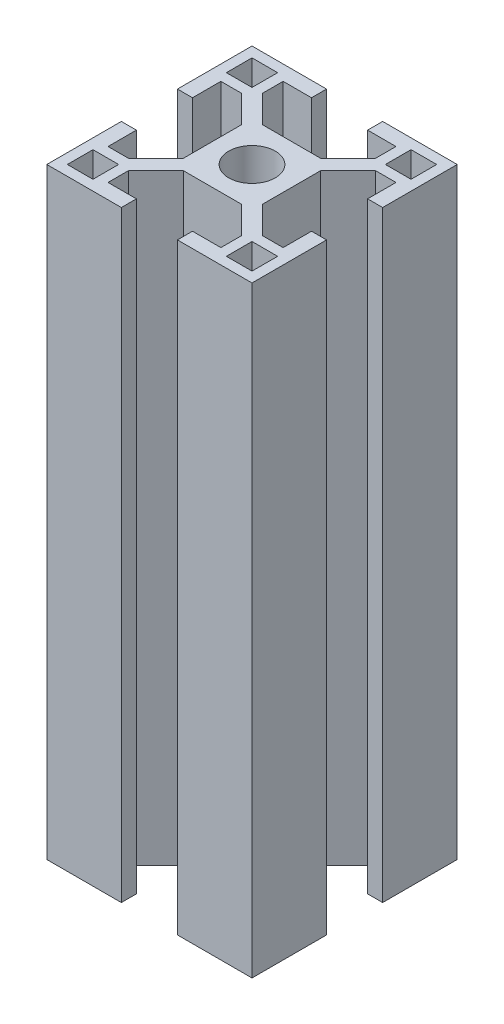
SolidWorks part; units mm, degrees
ref_plane "Płaszczyzna przednia" through (0, 0, 0) normal (0, 0, 1) x (1, 0, 0)
ref_plane "Płaszczyzna górna" through (0, 0, 0) normal (0, 1, 0) x (1, 0, 0)
ref_plane "Płaszczyzna prawa" through (0, 0, 0) normal (1, 0, 0) x (0, 0, -1)
sketch "Szkic1" plane through (0, 0, 0) normal (0, 1, 0) x (1, 0, 0)
  line L0 (4.1, 15) -> (4.1, 12.8)
  line L1 (-4.2444, -5.8) -> (4.2444, -5.8)
  line L2 (-5.8, -4.2444) -> (-5.8, 4.2444)
  line L3 (-4.2444, 5.8) -> (4.2444, 5.8)
  line L4 (5.8, -4.2444) -> (5.8, 4.2444)
  line L5 (-15, -15) -> (15, 15) construction
  line L6 (-15, 15) -> (15, -15) construction
  line L7 (4.1, 12.8) -> (8.25, 12.8)
  line L8 (8.25, 12.8) -> (8.25, 9.8056)
  line L9 (8.25, 9.8056) -> (4.2444, 5.8)
  line L10 (4.1, 15) -> (15, 15)
  line L11 (15, 15) -> (15, 4.1)
  line L12 (15, 4.1) -> (12.8, 4.1)
  line L13 (12.8, 4.1) -> (12.8, 8.25)
  line L14 (12.8, 8.25) -> (9.8056, 8.25)
  line L15 (9.8056, 8.25) -> (5.8, 4.2444)
  line L16 (-21.1799, 0) -> (30.3897, 0) construction
  line L17 (4.1, -15) -> (4.1, -12.8)
  line L18 (9.8056, -8.25) -> (5.8, -4.2444)
  line L19 (12.8, -8.25) -> (9.8056, -8.25)
  line L20 (12.8, -4.1) -> (12.8, -8.25)
  line L21 (15, -4.1) -> (12.8, -4.1)
  line L22 (15, -15) -> (15, -4.1)
  line L23 (4.1, -15) -> (15, -15)
  line L24 (8.25, -9.8056) -> (4.2444, -5.8)
  line L25 (8.25, -12.8) -> (8.25, -9.8056)
  line L26 (4.1, -12.8) -> (8.25, -12.8)
  line L27 (0, 19.5766) -> (0, -23.5143) construction
  line L28 (-4.1, 15) -> (-15, 15)
  line L29 (-4.1, 15) -> (-4.1, 12.8)
  line L30 (-8.25, 9.8056) -> (-4.2444, 5.8)
  line L31 (-8.25, 12.8) -> (-8.25, 9.8056)
  line L32 (-4.1, 12.8) -> (-8.25, 12.8)
  line L33 (-9.8056, 8.25) -> (-5.8, 4.2444)
  line L34 (-12.8, 8.25) -> (-9.8056, 8.25)
  line L35 (-12.8, 4.1) -> (-12.8, 8.25)
  line L36 (-15, 4.1) -> (-12.8, 4.1)
  line L37 (-15, 15) -> (-15, 4.1)
  line L38 (-15, -15) -> (-15, -4.1)
  line L39 (-15, -4.1) -> (-12.8, -4.1)
  line L40 (-12.8, -4.1) -> (-12.8, -8.25)
  line L41 (-4.1, -15) -> (-4.1, -12.8)
  line L42 (-4.1, -12.8) -> (-8.25, -12.8)
  line L43 (-8.25, -12.8) -> (-8.25, -9.8056)
  line L44 (-8.25, -9.8056) -> (-4.2444, -5.8)
  line L45 (-4.1, -15) -> (-15, -15)
  line L46 (-12.8, -8.25) -> (-9.8056, -8.25)
  line L47 (-9.8056, -8.25) -> (-5.8, -4.2444)
  line L48 (9.75, 11.625) -> (13.5, 11.625) construction
  line L49 (9.75, 9.75) -> (13.5, 9.75)
  line L50 (9.75, 9.75) -> (9.75, 13.5)
  line L51 (9.75, 13.5) -> (13.5, 13.5)
  line L52 (13.5, 9.75) -> (13.5, 13.5)
  line L53 (9.75, 9.75) -> (13.5, 13.5) construction
  line L54 (9.75, 13.5) -> (13.5, 9.75) construction
  line L55 (9.75, -9.75) -> (13.5, -9.75)
  line L56 (9.75, -9.75) -> (9.75, -13.5)
  line L57 (9.75, -13.5) -> (13.5, -13.5)
  line L58 (13.5, -9.75) -> (13.5, -13.5)
  line L59 (-9.75, -9.75) -> (-9.75, -13.5)
  line L60 (-9.75, -9.75) -> (-13.5, -9.75)
  line L61 (-13.5, -9.75) -> (-13.5, -13.5)
  line L62 (-9.75, -13.5) -> (-13.5, -13.5)
  line L63 (-9.75, 9.75) -> (-13.5, 9.75)
  line L64 (-9.75, 9.75) -> (-9.75, 13.5)
  line L65 (-9.75, 13.5) -> (-13.5, 13.5)
  line L66 (-13.5, 9.75) -> (-13.5, 13.5)
  circle A0 centre (0, 0) radius 3.4
  point P68 (0, 0)
  point P69 (11.625, 11.625)
  dimension "D1" = 6.8
  dimension "D2" = 30
  dimension "D3" = 30
  dimension "D4" = 16.5
  dimension "D5" = 8.2
  dimension "D6" = 8.2
  dimension "D7" = 16.5
  dimension "D8" = 9.2
  dimension "D9" = 2.2
  dimension "D10" = 135
  dimension "D11" = 2.2
  dimension "D12" = 2.2
  dimension "D13" = 3.75
  dimension "D14" = 3.75
  dimension "D15" = 4
extrude "Dodanie-wyciągnięcie1" add sketch "Szkic1" along normal blind 88 contours L47 L2 L33 L34 L35 L36 L37 L28 L29 L32 L31 L30 L3 L9 L8 L7 L0 L10 L11 L12 L13 L14 L15 L4 L18 L19 L20 L21 L22 L23 L17 L26 L25 L24 L1 L44 L43 L42 L41 L45 L38 L39 L40 L46
